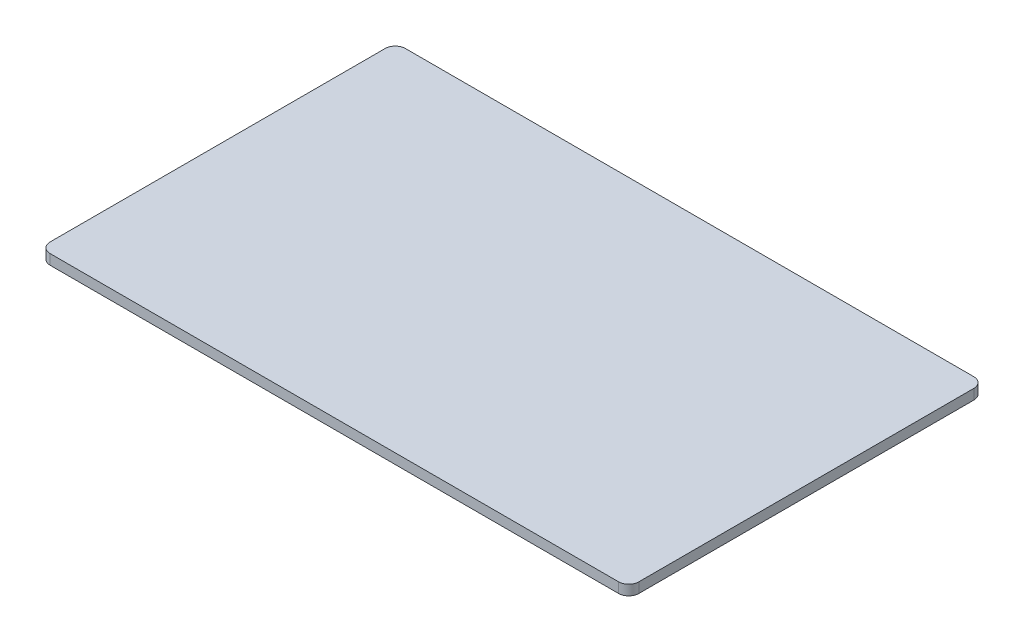
SolidWorks part; units mm, degrees
ref_plane "Front Plane" through (0, 0, 0) normal (0, 0, 1) x (1, 0, 0)
ref_plane "Top Plane" through (0, 0, 0) normal (0, 1, 0) x (1, 0, 0)
ref_plane "Right Plane" through (0, 0, 0) normal (1, 0, 0) x (0, 0, -1)
sketch "Sketch1" plane through (0, 0, 0) normal (0, 1, 0) x (1, 0, 0)
  line L0 (-73.66, 0) -> (73.66, 0)
  point P4 (0, 0)
extrude "Extrude-Thin1" add sketch "Sketch1" along normal blind 2.54 thin contours L0
fillet "Fillet1" radius 2.54 4 edges at (-73.66, 1.27, 0) (-73.66, 1.27, 88.9) (73.66, 1.27, 88.9) (73.66, 1.27, 0)
sketch "Sketch4" plane through (0, 2.54, 0) normal (0, 1, 0) x (1, 0, 0)
  line L0 (0, 0) -> (0, -25.4)
sketch "Sketch5" plane through (0, 2.54, 0) normal (0, 1, 0) x (1, 0, 0)
  line L0 (-6.35, -25.4) -> (6.35, -25.4)
  point P4 (0, -25.4)
sketch "Sketch6" plane through (0, 2.54, 0) normal (0, 1, 0) x (1, 0, 0)
  line L0 (-6.35, -25.4) -> (-6.35, 0)
  line L1 (-71.12, 0) -> (71.12, 0) construction
sketch "Sketch7" plane through (0, 2.54, 0) normal (0, 1, 0) x (1, 0, 0)
  line L0 (6.35, -25.4) -> (6.35, 0)
  line L1 (-71.12, 0) -> (71.12, 0) construction
